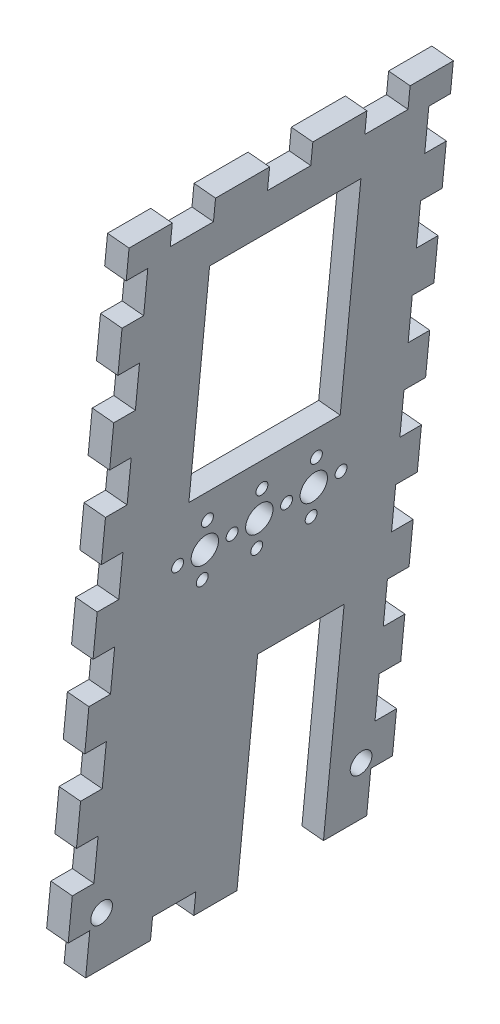
SolidWorks part; units mm, degrees
ref_plane "Front Plane" through (0, 0, 0) normal (0, 0, 1) x (1, 0, 0)
ref_plane "Top Plane" through (0, 0, 0) normal (0, 1, 0) x (1, 0, 0)
ref_plane "Right Plane" through (0, 0, 0) normal (1, 0, 0) x (0, 0, -1)
sketch "Sketch1" plane through (0, 0, 0) normal (0, 0, 1) x (1, 0, 0)
  line L0 (0, 0) -> (40.3547, 419.1) construction
  line L1 (40.3547, 419.1) -> (159.2585, 419.1) construction
  line L2 (159.2585, 419.1) -> (159.2585, 0) construction
  line L3 (159.2585, 0) -> (0, 0) construction
  line L4 (159.2585, -1000) -> (159.2585, 49000) construction
  line L5 (2.0164, 20.9415) -> (40.3547, 419.1) construction
  line L6 (2.0164, 20.9415) -> (41.8323, 17.1077) construction
  line L7 (40.3547, 419.1) -> (80.1706, 415.2662) construction
  line L8 (41.8323, 17.1077) -> (80.1706, 415.2662) construction
  line L9 (64.0085, -1000) -> (64.0085, 49000) construction
  line L10 (-49.0714, 317.5) -> (-124.9206, 324.8034) construction
  line L11 (-26.3513, 414.3375) -> (40.196, 414.3375) construction
  line L12 (-1162.1335, 304.8) -> (48837.8665, 304.8) construction
  line L13 (-126.4915, 292.1) -> (-50.2915, 292.1) construction
  line L14 (-124.9206, 324.8034) -> (-50.2915, 292.1) construction
  line L15 (-49.0714, 317.5) -> (-126.4915, 292.1) construction
  line L16 (40.196, 338.1375) -> (-26.3513, 338.1375) construction
  line L17 (-134.4017, 325.7164) -> (29.8401, 309.9017)
  line L18 (-134.4017, 325.7164) -> (-133.7931, 332.0371)
  line L19 (-133.7931, 332.0371) -> (40.3547, 419.1)
  line L20 (40.3547, 419.1) -> (108.4585, 419.1)
  line L21 (108.4585, 419.1) -> (108.4585, 0) construction
  line L22 (29.8401, 309.9017) -> (0.4102, 4.2603)
  line L23 (0.4102, 4.2603) -> (44.6556, 0)
  line L24 (44.6556, 0) -> (108.4585, 0)
  line L25 (108.4585, 419.1) -> (159.2585, 311.15)
  line L26 (159.2585, 311.15) -> (159.2585, 304.8)
  line L27 (159.2585, 304.8) -> (108.4585, 280.8941)
  line L28 (108.4585, 280.8941) -> (108.4585, 0)
  line L29 (0.4102, 4.2603) -> (0.9654, 10.0257)
  line L30 (0.4102, 4.2603) -> (44.9044, -0.024)
  line L31 (0.9654, 10.0257) -> (45.4596, 5.7414)
  line L32 (44.9044, -0.024) -> (45.4596, 5.7414)
  line L33 (39.1974, 6.9586) -> (45.5182, 6.35) construction
  arc A0 (-124.9206, 324.8034) -> (-26.3513, 414.3375) centre (-26.3513, 315.3123) cw construction
  arc A1 (73.5335, 304.8) -> (40.196, 338.1375) centre (40.196, 304.8) ccw construction
  arc A2 (149.7335, 304.8) -> (40.196, 414.3375) centre (40.196, 304.8) ccw construction
  arc A3 (-49.0714, 317.5) -> (-26.3513, 338.1375) centre (-26.3513, 315.3123) cw construction
  point P7 (57.6585, 400.05)
  point P10 (39.1388, 6.35)
  point P17 (149.7335, 304.8)
  point P18 (73.5335, 304.8)
  dimension "D9" = 9.525
  dimension "D14" = 25.4
  dimension "D1" = 419.1
  dimension "D2" = 101.6
  dimension "D3" = 19.05
  dimension "D4" = 19.05
  dimension "D5" = 84.5
  dimension "D6" = 40
  dimension "D7" = 400
  dimension "D8" = 95.25
  dimension "D10" = 9.525
  dimension "D11" = 114.3
  dimension "D12" = 76.2
  dimension "D13" = 9.525
  dimension "D15" = 127
  dimension "D16" = 9.525
  dimension "D17" = 209.55
  dimension "D18" = 6.35
  dimension "D19" = 50.8
  dimension "D20" = 44.45
  dimension "D21" = 6.35
  dimension "D22" = 44.7
  dimension "D23" = 6.35
  dimension "D24" = 6.35
  dimension "D25" = 6.35
  dimension "D26" = 6.35
sketch "Sketch2" plane through (0, 0, 0) normal (0, 0, 1) x (1, 0, 0)
  line L0 (38.5837, 0.5847) -> (44.9044, -0.024)
  line L1 (38.5837, 0.5847) -> (57.6878, 198.9884)
  line L2 (44.9044, -0.024) -> (64.0085, 198.3798)
  line L3 (57.6878, 198.9884) -> (64.0085, 198.3798)
  line L6 (0.4102, 4.2603) -> (44.6556, 0) construction
  line L7 (29.8401, 309.9017) -> (0.4102, 4.2603) construction
  line L8 (64.0085, -201000) -> (64.0085, 249000) construction
  dimension "D1" = 6.35
  dimension "D2" = 38.35
extrude "Boss-Extrude1" add sketch "Sketch2" along normal blind 95.25
sketch "Sketch3" plane through (38.1734, -3.6757, 0) normal (-0.9954, 0.0958, 0) x (0, 0, 1)
  line L0 (95.25, 4.28) -> (0, 4.28) construction
  line L1 (85.725, -11.595) -> (9.525, -11.595) construction
  line L2 (85.725, -11.595) -> (85.725, 20.155) construction
  line L3 (85.725, 20.155) -> (9.525, 20.155) construction
  line L4 (9.525, -11.595) -> (9.525, 20.155) construction
  line L5 (85.725, -11.595) -> (9.525, 20.155) construction
  line L6 (85.725, 20.155) -> (9.525, -11.595) construction
  line L7 (0, 203.6014) -> (0, 4.28) construction
  circle A0 centre (9.525, 20.155) radius 3.175
  circle A1 centre (85.725, 20.155) radius 3.175
  point P0 (47.625, 4.28)
  dimension "D2" = 6.35
  dimension "D1" = 15.875
  dimension "D3" = 9.525
extrude "Cut-Extrude1" cut sketch "Sketch3" against normal through all
sketch "Sketch4" plane through (38.1734, -3.6757, 0) normal (-0.9954, 0.0958, 0) x (0, 0, 1)
  line L0 (47.625, -995.72) -> (47.625, 49004.28) construction
  line L1 (95.25, 4.28) -> (0, 4.28) construction
  circle A0 centre (47.625, 105.88) radius 4
  circle A1 centre (47.625, 113.88) radius 1.75
  circle A2 centre (55.625, 105.88) radius 1.75
  circle A3 centre (47.625, 97.88) radius 1.75
  circle A4 centre (39.625, 105.88) radius 1.75
  point P5 (47.625, 4.28)
  point P18 (47.625, 105.88)
  dimension "D3" = 3.5
  dimension "D4" = 8
  dimension "D1" = 101.6
  dimension "D2" = 8
  dimension "D5" = 4
extrude "Cut-Extrude2" cut sketch "Sketch4" against normal through all
pattern_linear "LPattern1" count 2 spacing 16 along (0, 0, 1) count 2 spacing 16 along (0, 0, -1) of "Cut-Extrude2"
sketch "Sketch5" plane through (38.1734, -3.6757, 0) normal (-0.9954, 0.0958, 0) x (0, 0, 1)
  line L0 (0, 203.6014) -> (0, 4.28) construction
  line L1 (25.4, 185.38) -> (69.85, 185.38)
  line L2 (25.4, 185.38) -> (25.4, 121.88)
  line L3 (25.4, 121.88) -> (69.85, 121.88)
  line L4 (69.85, 185.38) -> (69.85, 121.88)
  line L5 (95.25, 203.6014) -> (95.25, 4.28) construction
  circle A0 centre (63.625, 105.88) radius 4 construction
  dimension "D3" = 16
  dimension "D1" = 25.4
  dimension "D2" = 25.4
  dimension "D4" = 63.5
extrude "Cut-Extrude3" cut sketch "Sketch5" against normal through all
sketch "Sketch6" plane through (38.1734, -3.6757, 0) normal (-0.9954, 0.0958, 0) x (0, 0, 1)
  line L0 (95.25, 4.28) -> (0, 4.28) construction
  line L1 (19.05, 4.28) -> (44.45, 4.28)
  line L2 (19.05, 4.28) -> (19.05, 67.78)
  line L3 (19.05, 67.78) -> (44.45, 67.78)
  line L4 (44.45, 4.28) -> (44.45, 67.78)
  line L5 (31.75, 67.78) -> (0, 67.78) construction
  line L6 (0, 203.6014) -> (0, 4.28) construction
  dimension "D1" = 63.5
  dimension "D2" = 25.4
  dimension "D3" = 31.75
extrude "Cut-Extrude4" cut sketch "Sketch6" against normal through all
sketch "Sketch8" plane through (38.1734, -3.6757, 0) normal (-0.9954, 0.0958, 0) x (0, 0, 1)
  line L0 (19.05, 4.28) -> (0, 4.28) construction
  line L1 (6.35, 4.28) -> (0, 4.28)
  line L2 (6.35, 4.28) -> (6.35, 16.98)
  line L3 (6.35, 16.98) -> (0, 16.98)
  line L4 (0, 4.28) -> (0, 16.98)
  line L5 (0, 203.6014) -> (0, 4.28) construction
  line L7 (95.25, 4.28) -> (88.9, 4.28)
  line L8 (95.25, 4.28) -> (95.25, 16.98)
  line L9 (95.25, 16.98) -> (88.9, 16.98)
  line L10 (88.9, 4.28) -> (88.9, 16.98)
  dimension "D1" = 12.7
  dimension "D2" = 6.35
extrude "Cut-Extrude6" cut sketch "Sketch8" against normal through all
pattern_linear "LPattern2" count 18 spacing 25.4 along (0.0958, 0.9954, 0) of "Cut-Extrude6"
sketch "Sketch9" plane through (38.1734, -3.6757, 0) normal (-0.9954, 0.0958, 0) x (0, 0, 1)
  line L0 (88.9, 4.28) -> (44.45, 4.28) construction
  line L1 (57.15, 4.28) -> (69.85, 4.28)
  line L2 (57.15, 4.28) -> (57.15, 10.6835)
  line L3 (57.15, 10.6835) -> (69.85, 10.6835)
  line L4 (69.85, 4.28) -> (69.85, 10.6835)
  line L5 (95.25, 29.68) -> (95.25, 16.98) construction
  dimension "D1" = 25.4
  dimension "D2" = 12.7
extrude "Cut-Extrude7" cut sketch "Sketch9" against normal through all
sketch "Sketch10" plane through (38.1734, -3.6757, 0) normal (-0.9954, 0.0958, 0) x (0, 0, 1)
  line L0 (95.25, 203.6014) -> (0, 203.6014) construction
  line L1 (12.7, 203.6014) -> (25.4, 203.6014)
  line L2 (12.7, 203.6014) -> (12.7, 197.2514)
  line L3 (12.7, 197.2514) -> (25.4, 197.2514)
  line L4 (25.4, 203.6014) -> (25.4, 197.2514)
  line L5 (0, 203.6014) -> (0, 194.78) construction
  line L6 (41.275, 203.6014) -> (53.975, 203.6014)
  line L7 (41.275, 203.6014) -> (41.275, 197.2514)
  line L8 (41.275, 197.2514) -> (53.975, 197.2514)
  line L9 (53.975, 203.6014) -> (53.975, 197.2514)
  line L10 (69.85, 203.6014) -> (82.55, 203.6014)
  line L11 (69.85, 203.6014) -> (69.85, 197.2514)
  line L12 (69.85, 197.2514) -> (82.55, 197.2514)
  line L13 (82.55, 203.6014) -> (82.55, 197.2514)
  line L14 (95.25, 203.6014) -> (95.25, 194.78) construction
  line L15 (47.625, 197.2514) -> (47.625, 185.38) construction
  line L16 (69.85, 185.38) -> (25.4, 185.38) construction
  dimension "D1" = 12.7
  dimension "D2" = 12.7
  dimension "D3" = 12.7
  dimension "D4" = 6.35
extrude "Cut-Extrude8" cut sketch "Sketch10" against normal through all
